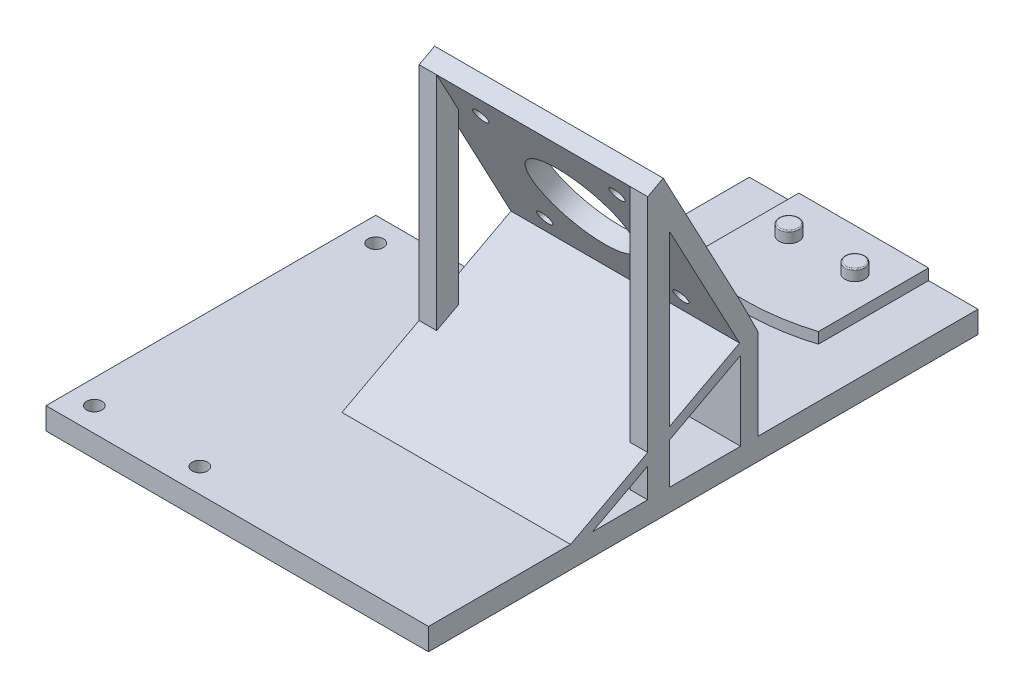
SolidWorks part; units mm, degrees
ref_plane "Front Plane" through (0, 0, 0) normal (0, 0, 1) x (1, 0, 0)
ref_plane "Top Plane" through (0, 0, 0) normal (0, 1, 0) x (1, 0, 0)
ref_plane "Right Plane" through (0, 0, 0) normal (1, 0, 0) x (0, 0, -1)
sketch "Sketch1" plane through (0, 0, 0) normal (0, 1, 0) x (1, 0, 0)
  line L1 (26, 50) -> (-26, 50)
  line L2 (26, 50) -> (26, -50)
  line L3 (26, -50) -> (-26, -50)
  line L4 (-26, 50) -> (-26, -50)
  line L5 (26, 50) -> (-26, -50) construction
  line L6 (26, -50) -> (-26, 50) construction
  point P0 (0, 0)
  dimension "D1" = 52
  dimension "D2" = 100
extrude "Boss-Extrude1" add sketch "Sketch1" along normal blind 5
sketch "Sketch2" plane through (0, 5, 0) normal (0, 1, 0) x (1, 0, 0)
  line L0 (26, -50) -> (26, 50) construction
  line L1 (-26, 50) -> (26, 50)
  line L2 (-26, 50) -> (-26, 30)
  line L4 (26, 50) -> (26, 30)
  line L5 (0, 0) -> (0, 72.7083) construction
  line L6 (0, 72.7083) -> (-26, 30) construction
  arc A0 (-26, 30) -> (26, 30) centre (0, 72.7083) ccw
  dimension "D1" = 20
  dimension "D2" = 50
extrude "Boss-Extrude3" add sketch "Sketch2" along normal blind 2.5
sketch "Sketch7" plane through (0, 7.5, 0) normal (0, 1, 0) x (1, 0, 0)
  line L1 (26, 50) -> (-26, 50) construction
  circle A0 centre (-7.5, 40.5) radius 2.25
  circle A1 centre (7.5, 40.5) radius 2.25
  dimension "D1" = 4.5
  dimension "D2" = 4.5
  dimension "D3" = 7.5
  dimension "D4" = 7.5
  dimension "D5" = 9.5
  dimension "D6" = 9.5
extrude "Boss-Extrude4" add sketch "Sketch7" along normal blind 2.5
fillet "Fillet2" radius 0.25 2 edges at (7.5, 10, -38.25) (-7.5, 10, -38.25)
sketch "Sketch9" plane through (0, 5, 0) normal (0, 1, 0) x (1, 0, 0)
  line L0 (26, 0) -> (-26, 0)
  line L1 (26, -50) -> (26, 30) construction
  line L2 (-26, 30) -> (-26, -50) construction
  line L3 (-26, 0) -> (-26, -4)
  line L4 (-26, -4) -> (26, -4)
  line L5 (26, -4) -> (26, 0)
  line L7 (26, 50) -> (-26, 50) construction
  dimension "D1" = 4
  dimension "D2" = 54
extrude "Boss-Extrude5" add sketch "Sketch9" along normal blind 50
sketch "Sketch10" plane through (-26, 0, 0) normal (-1, 0, 0) x (0, 0, 1)
  line L0 (4, 25) -> (25.1262, 64.7326)
  line L1 (4, 55) -> (4, 5) construction
  line L2 (25.1262, 64.7326) -> (21.5944, 66.6105)
  line L3 (21.5944, 66.6105) -> (4, 33.5202)
  line L4 (4, 33.5202) -> (4, 25)
  line L5 (4, 5) -> (50, 5) construction
  dimension "D1" = 28
  dimension "D2" = 4
  dimension "D3" = 20
  dimension "D4" = 45
extrude "Boss-Extrude7" add sketch "Sketch10" against normal up to surface (52 mm away) up to face at (26, 14.5, -5.2)
sketch "Sketch11" plane through (-26, 0, 0) normal (-1, 0, 0) x (0, 0, 1)
  line L0 (4, 33.5202) -> (0, 25.4987)
  line L1 (0, 55) -> (0, 5) construction
  line L2 (0, 25.4987) -> (0, 55)
  line L3 (0, 55) -> (4, 55)
  line L4 (4, 55) -> (4, 33.5202)
extrude "Cut-Extrude3" cut sketch "Sketch11" against normal up to surface (52 mm away) up to face at (26, 23.9188, 0.1943)
sketch "Sketch13" plane through (0, 7.5, 0) normal (0, 1, 0) x (1, 0, 0)
  line L0 (-14.75, 50) -> (14.75, 50) construction
  line L1 (26, 50) -> (-26, 50) construction
  line L2 (-14.75, 50) -> (-14.75, 24.9335)
  line L3 (-14.75, 50) -> (-26, 50)
  line L4 (-26, 50) -> (-26, 30)
  line L5 (26, 30) -> (26, 50)
  line L6 (26, 50) -> (14.75, 50)
  line L7 (14.75, 50) -> (14.75, 24.9335)
  line L8 (0, 22.7083) -> (0, 72.7083) construction
  line L9 (0, 72.7083) -> (-26, 30) construction
  arc A0 (-26, 30) -> (26, 30) centre (0, 72.7083) ccw construction
  arc A1 (-26, 30) -> (26, 30) centre (0, 72.7083) ccw construction
  arc A2 (-26, 30) -> (-14.75, 24.9335) centre (0, 72.7083) ccw
  arc A3 (26, 30) -> (14.75, 24.9335) centre (0, 72.7083) cw
  line M9 (-26, 50) -> (-26, 30)
  arc M10 (-26, 30) -> (26, 30) centre (0, 72.7083) ccw
  line M11 (26, 30) -> (26, 50)
  line M12 (26, 50) -> (-26, 50)
  dimension "D1" = 29.5
  dimension "D2" = 14.75
  dimension "D3" = 50
extrude "Cut-Extrude4" cut sketch "Sketch13" against normal blind 2.5 contours L2 M12 M9 M10 | L7 M12 M10 M11
sketch "Sketch16" plane through (-26, 0, 0) normal (-1, 0, 0) x (0, 0, 1)
  line L0 (4.2347, 25.4415) -> (42.6796, 5)
  line L4 (4, 25) -> (25.1262, 64.7326) construction
  line L8 (4, 25) -> (4.2347, 25.4415)
  line L11 (4, 5) -> (50, 5) construction
  line L14 (42.6796, 5) -> (37.6796, 5)
  line L15 (37.6796, 5) -> (4, 22.9077)
  line L16 (4, 25) -> (4, 5) construction
  line L17 (4, 25) -> (4, 22.9077)
  dimension "D1" = 90
  dimension "D2" = 5
  dimension "D3" = 0.5
extrude "Boss-Extrude8" add sketch "Sketch16" against normal up to surface (52 mm away) up to face at (26, 21.3965, 5.3382)
sketch "Sketch17" plane through (-26, 0, 0) normal (-1, 0, 0) x (0, 0, 1)
  line L0 (25.1262, 64.7326) -> (25.1262, 5)
  line L1 (4, 5) -> (37.6796, 5) construction
  line L6 (25.1262, 64.7326) -> (20.1262, 55.329)
  line L7 (4.2347, 25.4415) -> (25.1262, 64.7326) construction
  line L8 (20.1262, 55.329) -> (20.1262, 5)
  line L9 (4, 5) -> (37.6796, 5) construction
  line L10 (20.1262, 5) -> (25.1262, 5)
  dimension "D1" = 5
extrude "Boss-Extrude9" add sketch "Sketch17" against normal blind 4
pattern_linear "LPattern1" count 2 spacing 48 along (1, 0, 0) of "Boss-Extrude9"
sketch "Sketch18" plane through (0, 5.7299, -10.7764) normal (0, 0.4695, -0.8829) x (-1, 0, 0)
  line L0 (-26, 68.9516) -> (26, 68.9516) construction
  circle A0 centre (0, 45.9516) radius 11.5
  dimension "D1" = 23
  dimension "D2" = 23
extrude "Cut-Extrude5" cut sketch "Sketch18" against normal up to surface (4 mm away) up to face at (0, 50.208, 17.4033)
hole_wizard "CSK for M3 Countersunk Flat Head Screw1" positions "Sketch20" profile "Sketch21" countersink size "M3" standard "ISO"
sketch "Sketch20" plane through (0, 5.7299, -10.7764) normal (0, 0.4695, -0.8829) x (-1, 0, 0)
  line L0 (0, 68.9516) -> (0, 22.9543) construction
  line L1 (-26, 68.9516) -> (26, 68.9516) construction
  line L2 (-26, 22.9543) -> (26, 22.9543) construction
  line L7 (-26, 45.9516) -> (26, 45.9516) construction
  line L8 (-26, 31.4745) -> (-26, 68.9516) construction
  line L9 (26, 68.9516) -> (26, 31.4745) construction
  point P0 (-15.5, 61.4516)
  point P2 (15.5, 61.4516)
  point P4 (15.5, 30.4516)
  point P6 (-15.5, 30.4516)
  dimension "D1" = 15.5
  dimension "D2" = 15.5
  dimension "D3" = 15.5
  dimension "D4" = 15.5
  dimension "D5" = 15.5
  dimension "D6" = 15.5
  dimension "D7" = 15.5
  dimension "D8" = 15.5
sketch "Sketch21" plane through (15.5, 59.9884, 18.0734) normal (1, 0, 0) x (0, 0.8829, 0.4695)
  line L0 (0, 0) -> (0, 6.0215)
  line L1 (0, 6.0215) -> (1.7, 5)
  line L2 (1.7, 5) -> (1.7, 1.45)
  line L3 (1.7, 1.45) -> (3.15, 0)
  line L5 (3.15, 0) -> (0, 0)
  line L6 (-1.7, 1.45) -> (-3.15, 0) construction
  line L10 (0, 6.0215) -> (-1.7, 5) construction
  line L11 (0, -6.35) -> (0, 107.95) construction
  dimension "Hole Dia." = 3.4
  dimension "Hole Depth" = 5
  dimension "Near C'Sink Dia." = 6.3
  dimension "Near C'Sink Angle" = 90
  dimension "Drill Angle" = 118
sketch "Sketch22" plane through (0, 0, 0) normal (0, -1, 0) x (1, 0, 0)
  line L3 (26, 75) -> (-61, 75)
  line L4 (-61, 0) -> (-61, 75)
  line L6 (-26, -50) -> (-26, 50) construction
  line L7 (-26, 50) -> (26, 50) construction
  line L8 (-26, 0) -> (-26, 50)
  line L9 (-26, 50) -> (26, 50)
  line L10 (-61, 0) -> (-26, 0)
  line L11 (26, 50) -> (26, 75)
  dimension "D1" = 35
  dimension "D2" = 25
  dimension "D3" = 75
extrude "Boss-Extrude10" add sketch "Sketch22" against normal blind 5
sketch "Sketch23" plane through (0, 5, 0) normal (0, 1, 0) x (1, 0, 0)
  line L0 (-28.5, -2.5) -> (-28.5, -72.5) construction
  line L1 (-28.5, -72.5) -> (-58.5, -72.5) construction
  line L2 (-58.5, -72.5) -> (-58.5, -2.5) construction
  line L3 (-58.5, -2.5) -> (-28.5, -2.5) construction
  line L4 (-61, 0) -> (-26, 0) construction
  line L6 (-61, -75) -> (-61, 0) construction
  circle A0 centre (-31.5, -5.5) radius 1.75
  circle A1 centre (-55.5, -5.5) radius 1.75
  circle A2 centre (-55.5, -69.5) radius 1.75
  circle A3 centre (-31.5, -69.5) radius 1.75
  dimension "D5" = 3
  dimension "D6" = 3.5
  dimension "D7" = 3
  dimension "D8" = 3.5
  dimension "D9" = 3
  dimension "D10" = 3
  dimension "D11" = 3
  dimension "D12" = 3.5
  dimension "D13" = 3
  dimension "D14" = 3
  dimension "D15" = 3.5
  dimension "D16" = 3
  dimension "D1" = 30
  dimension "D2" = 70
  dimension "D3" = 2.5
  dimension "D4" = 2.5
extrude "Cut-Extrude6" cut sketch "Sketch23" against normal blind 5
sketch "Sketch24" plane through (0, 0, 0) normal (0, -1, 0) x (1, 0, 0)
  line L1 (-28.2, 66.7) -> (-34.8, 66.7)
  line L2 (-28.2, 66.7) -> (-28.2, 72.3)
  line L3 (-28.2, 72.3) -> (-34.8, 72.3)
  line L4 (-34.8, 66.7) -> (-34.8, 72.3)
  line L5 (-28.2, 66.7) -> (-34.8, 72.3) construction
  line L6 (-28.2, 72.3) -> (-34.8, 66.7) construction
  line L7 (-52.2, 66.7) -> (-58.8, 66.7)
  line L8 (-52.2, 66.7) -> (-52.2, 72.3)
  line L9 (-52.2, 72.3) -> (-58.8, 72.3)
  line L10 (-58.8, 66.7) -> (-58.8, 72.3)
  line L11 (-52.2, 66.7) -> (-58.8, 72.3) construction
  line L12 (-52.2, 72.3) -> (-58.8, 66.7) construction
  line L13 (-28.2, 2.7) -> (-34.8, 2.7)
  line L14 (-28.2, 2.7) -> (-28.2, 8.3)
  line L15 (-28.2, 8.3) -> (-34.8, 8.3)
  line L16 (-34.8, 2.7) -> (-34.8, 8.3)
  line L17 (-28.2, 2.7) -> (-34.8, 8.3) construction
  line L18 (-28.2, 8.3) -> (-34.8, 2.7) construction
  line L19 (-52.2, 2.7) -> (-58.8, 2.7)
  line L20 (-52.2, 2.7) -> (-52.2, 8.3)
  line L21 (-52.2, 8.3) -> (-58.8, 8.3)
  line L22 (-58.8, 2.7) -> (-58.8, 8.3)
  line L23 (-52.2, 2.7) -> (-58.8, 8.3) construction
  line L24 (-52.2, 8.3) -> (-58.8, 2.7) construction
  point P0 (-31.5, 69.5)
  point P6 (-55.5, 69.5)
  point P12 (-31.5, 5.5)
  point P18 (-55.5, 5.5)
  dimension "D1" = 5.6
  dimension "D2" = 6.6
  dimension "D3" = 5.6
  dimension "D4" = 6.6
  dimension "D5" = 5.6
  dimension "D6" = 6.6
  dimension "D7" = 5.6
  dimension "D8" = 6.6
extrude "Cut-Extrude7" cut sketch "Sketch24" against normal blind 2.5
